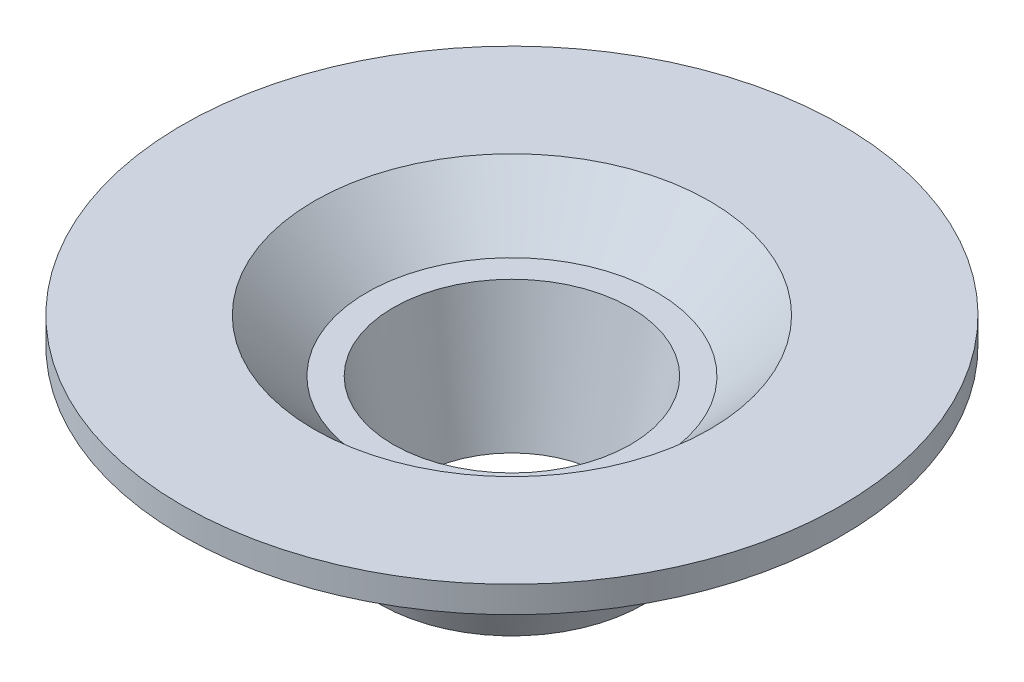
SolidWorks part; units mm, degrees
ref_plane "Front Plane" through (0, 0, 0) normal (0, 0, 1) x (1, 0, 0)
ref_plane "Top Plane" through (0, 0, 0) normal (0, 1, 0) x (1, 0, 0)
ref_plane "Right Plane" through (0, 0, 0) normal (1, 0, 0) x (0, 0, -1)
sketch "Sketch1" plane through (0, 0, 0) normal (1, 0, 0) x (0, 0, -1)
  line L0 (0, 0) -> (0, -5) construction
  line L1 (4.5, 0) -> (3.5, -5)
  line L2 (3.5, -5) -> (5, -5)
  line L3 (5, -5) -> (6.5, -1)
  line L4 (6.5, -1) -> (8.5, -1)
  line L5 (8.5, -1) -> (10.5, 1)
  line L6 (10.5, 1) -> (12.5, 1)
  line L7 (12.5, 1) -> (12.5, 2)
  line L8 (12.5, 2) -> (7.5, 2)
  line L9 (7.5, 2) -> (5.5, 0)
  line L10 (5.5, 0) -> (4.5, 0)
  point P3 (0, 0)
  point P14 (0, 0)
  dimension "D1" = 5
  dimension "D2" = 3.5
  dimension "D3" = 1.5
  dimension "D4" = 6.5
  dimension "D5" = 4.5
  dimension "D6" = 1
  dimension "D7" = 12.5
  dimension "D8" = 2
  dimension "D9" = 2
  dimension "D10" = 2
  dimension "D11" = 4
  dimension "D12" = 1
revolve "Revolve1" add sketch "Sketch1" angle 360 about L0
